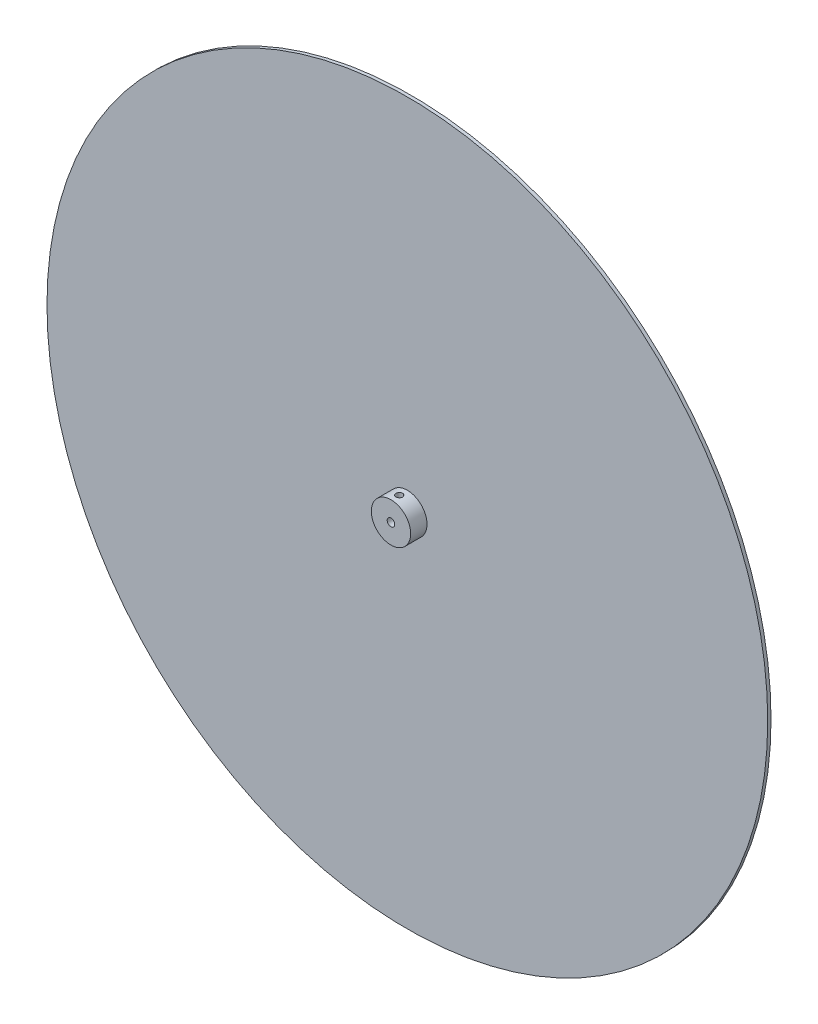
SolidWorks part; units mm, degrees
ref_plane "前视基准面" through (0, 0, 0) normal (0, 0, 1) x (1, 0, 0)
ref_plane "上视基准面" through (0, 0, 0) normal (0, 1, 0) x (1, 0, 0)
ref_plane "右视基准面" through (0, 0, 0) normal (1, 0, 0) x (0, 0, -1)
sketch "草图1" plane through (0, 0, 0) normal (0, 0, 1) x (1, 0, 0)
  circle A0 centre (0, 0) radius 110
  circle A1 centre (0, 0) radius 1.15
  dimension "D1" = 2.3
  dimension "D2" = 220
extrude "凸台-拉伸1" add sketch "草图1" along normal blind 1
sketch "草图2" plane through (0, 0, 0) normal (0, 0, -1) x (-1, 0, 0)
  circle A0 centre (0, 0) radius 1.15
  circle A1 centre (0, 0) radius 6
  dimension "D1" = 2.3
  dimension "D2" = 12
extrude "凸台-拉伸2" add sketch "草图2" along normal blind 5 and the other way blind 6
sketch "草图3" plane through (0, 0, 0) normal (0, 1, 0) x (1, 0, 0)
  line L0 (0, 2.5) -> (0, 0) construction
  line L1 (0, 0) -> (0, -3.5) construction
  line L2 (-6, -1) -> (6, -1) construction
  circle A0 centre (0, 2.5) radius 1
  circle A1 centre (0, -3.5) radius 1
  dimension "D1" = 2
  dimension "D3" = 2.5
  dimension "D2" = 2.5
extrude "切除-拉伸1" cut sketch "草图3" against normal mid plane 50
cosmetic thread "装饰螺纹线1" parameters "D1"=2.4, "D2"=2.5
cosmetic thread "装饰螺纹线2" parameters "D1"=2.4, "D2"=2.5
